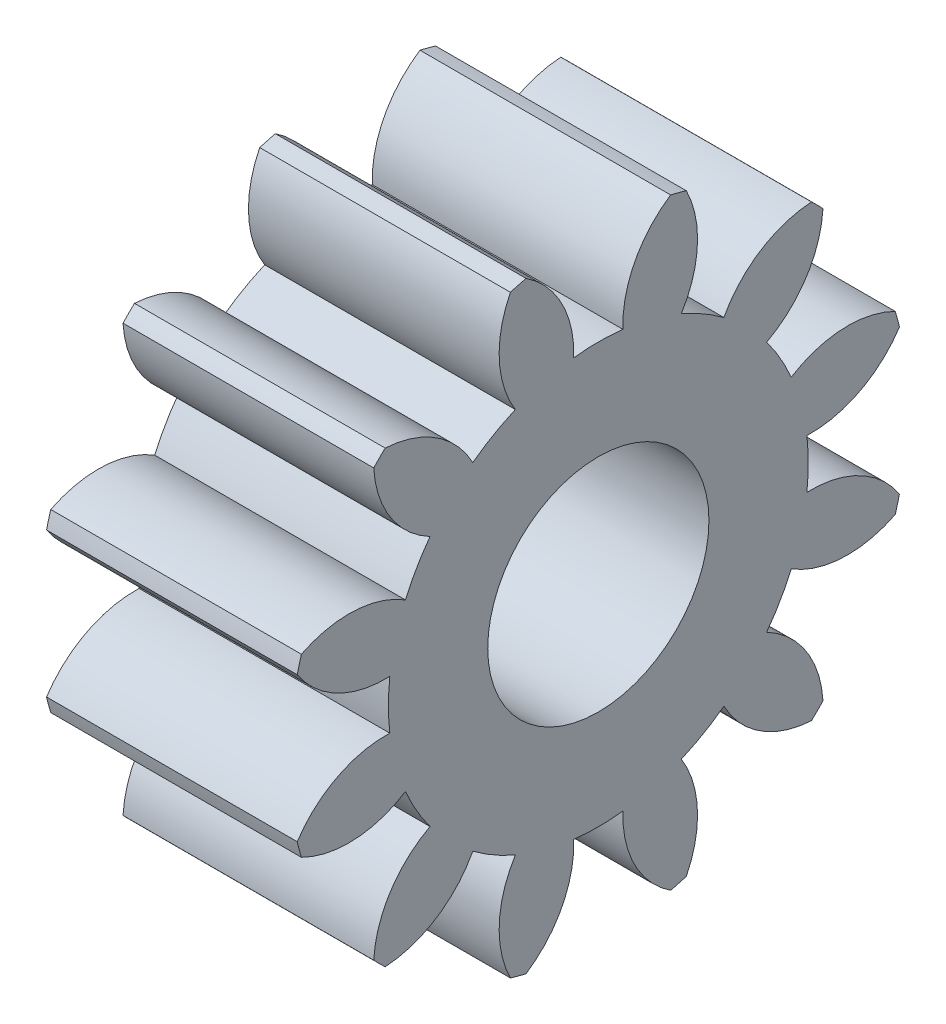
SolidWorks part; units mm, degrees
ref_plane "Plane1" through (0, 0, 0) normal (0, 0, 1) x (1, 0, 0)
ref_plane "Plane2" through (0, 0, 0) normal (0, 1, 0) x (1, 0, 0)
ref_plane "Plane3" through (0, 0, 0) normal (1, 0, 0) x (0, 0, -1)
sketch "HoldingSke" plane through (0, 0, 0) normal (0, 1, 0) x (1, 0, 0)
  line L0 (0, 0) -> (3.2605, -0.693)
  line L1 (-15, 0) -> (100, 0) construction
  line L2 (0, 0) -> (-2.1039, 2.3779)
  line L3 (0, 0) -> (-11.863, 4.5341)
  line L4 (0, 0) -> (8.4473, 1.7955)
  line L5 (0, 0) -> (-46.8476, -17.4728)
  line L6 (0, 0) -> (-1.4092, -0.9508)
  line L7 (-2.1039, 2.3779) -> (8.6586, 51.2059)
  line L8 (-76.2, 54.61) -> (-76, 54.61)
  line L9 (-71.009, 38.7566) -> (-53.1078, 45.2721)
  line L10 (-76.2, 71.12) -> (104.1128, 71.12)
  line L11 (0, 0) -> (-1.7, 0)
  line L12 (-76.2, 101.6) -> (-76.19, 101.6)
  line L13 (24.9733, 27.94) -> (52.9518, 28.4284)
  line L14 (24.9733, 27.94) -> (24.9743, 27.94)
  line L15 (24.9733, 27.94) -> (100.4006, 29.5858)
  line L16 (-63.627, -0.3) -> (-12.827, -0.3)
  circle A0 centre (0, 0) radius 0.75
  circle A1 centre (0, 0) radius 1.424
  circle A2 centre (0, 0) radius 37.5
  circle A3 centre (0, 0) radius 0.75
  dimension "MHD" = 2.848
  dimension "Hub_dia" = 75
  dimension "Bore" = 1.5
  dimension "MBD" = 1.5
  dimension "Num_teeth" = 12
  dimension "Pitch" = 3.3333
  dimension "Overall_len" = 50
  dimension "Show_teeth" = 12
  dimension "Thickness" = 1.7
  dimension "OAL" = 50.0001
  dimension "T_dim" = 0.2
  dimension "Ap" = 20
  dimension "H" = 19.05
  dimension "Pitch_radius" = 180.3128
  dimension "Width" = 1.7
  dimension "Backlash" = 0.01
  dimension "Addendum_fac" = 1
  dimension "Dedendum_fac" = 1.25
  dimension "Clearance_fac" = 0.25
  dimension "Dedendum_add" = 0.001
  dimension "Module" = 0.3
sketch "BasProSke" plane through (0, 0, 0) normal (0, 1, 0) x (1, 0, 0)
  line L0 (-10, 0) -> (60, 0) construction
  line L1 (0, 0) -> (0, 2.1)
  line L2 (0, 0) -> (1.7, 0)
  line L3 (1.7, 0) -> (1.7, 2.1)
  line L4 (1.7, 2.1) -> (0, 2.1)
  dimension "Thickness" = 1.7
  dimension "Diameter" = 4.2
revolve "Base-Revolve" add sketch "BasProSke" angle 360 about L0
sketch "TooCutSke" plane through (0, 0, 0) normal (1, 0, 0) x (0, 0, -1)
  line L1 (0, 0) -> (0, 107) construction
  line L2 (0, 0) -> (-0.2524, 1.7822) construction
  line L3 (0, 0) -> (-0.9249, 3.4519) construction
  line L4 (-0.2524, 1.7822) -> (-0.4625, 1.7259) construction
  arc A0 (0.1667, 1.4142) -> (-0.1667, 1.4142) centre (0, 0) ccw
  arc A1 (0.5203, 2.0607) -> (-0.5203, 2.0607) centre (0, 0) ccw
  circle A2 centre (0, 0) radius 1.8 construction
  circle A3 centre (0, 0) radius 1.6914 construction
  arc A4 (-0.1667, 1.4142) -> (-0.5203, 2.0607) centre (-0.8863, 1.4407) ccw
  arc A5 (0.5203, 2.0607) -> (0.1667, 1.4142) centre (0.8863, 1.4407) ccw
  dimension "Root_dia" = 2.848
  dimension "Overcut_dia" = 4.2508
  dimension "Pitch_dia" = 3.6
  dimension "Base_dia" = 3.3829
  dimension "Flank_rad" = 0.72
  dimension "Half_ang" = 15
  dimension "Half_CT" = 0.2174
extrude "ToothCut" cut sketch "TooCutSke" along normal through all
fillet "Breaks" [suppressed] radius 0.006
fillet "RootFillets" [suppressed] radius 0.076
pattern_circular "TeethCuts" count 12 every 30 about axis through (-10, 0, 0) along (1, 0, 0) of "ToothCut", "RootFillets", "Breaks"
sketch "HubNeaOneSke" plane through (0, 0, 0) normal (-1, 0, 0) x (0, 0, 1)
  circle A0 centre (0, 0) radius 1.424
  dimension "Diameter" = 2.848
extrude "HubNearOne" [suppressed] add sketch "HubNeaOneSke" along normal blind 48.3001
sketch "HubNeaBotSke" plane through (0, 0, 0) normal (-1, 0, 0) x (0, 0, 1)
  circle A0 centre (0, 0) radius 1.424
  dimension "Diameter" = 2.848
extrude "HubNearBoth" [suppressed] add sketch "HubNeaBotSke" along normal blind 24.15
ref_plane "FarPln" through (1.7, 0, 0) normal (1, 0, 0) x (0, 0, -1)
sketch "HubFarSke" plane through (1.7, 0, 0) normal (1, 0, 0) x (0, 0, -1)
  circle A0 centre (0, 0) radius 1.424
  dimension "Diameter" = 2.848
extrude "HubFar" [suppressed] add sketch "HubFarSke" along normal blind 24.15
sketch "BorSke" plane through (0, 0, 0) normal (1, 0, 0) x (0, 0, -1)
  circle A0 centre (0, 0) radius 0.75
  dimension "Diameter" = 1.5
extrude "Bore" cut sketch "BorSke" along normal mid plane 100.0001
sketch "KeySke" plane through (0, 0, 0) normal (1, 0, 0) x (0, 0, -1)
  line L0 (-0.3, 0) -> (-0.3, 0.95)
  line L1 (-0.3, 0.95) -> (0.3, 0.95)
  line L2 (0.3, 0.95) -> (0.3, 0)
  line L3 (0, 0) -> (0, 34) construction
  line L4 (-0.3, 0) -> (0.3, 0)
  dimension "Offset" = 0.95
  dimension "Width" = 0.6
extrude "Keyway" [suppressed] cut sketch "KeySke" along normal mid plane 100.0001
pattern_circular "Keyway2" [suppressed] count 2 every 90 about axis through (-10, 0, 0) along (1, 0, 0)
equation "' \"Module@HoldingSke\" = 6.35"
equation "' \"Num_teeth@HoldingSke\" = 12"
equation "' \"Ap@HoldingSke\" =  20"
equation "' \"Ap@HoldingSke\" = 20"
equation "' \"Width@HoldingSke\" = 0.5 * 25.4"
equation "' \"Hub_dia@HoldingSke\"= 1 * 25.4"
equation "' \"Hub_dia@HoldingSke\" = 1 * 25.4"
equation "' \"Overall_len@HoldingSke\" = 1.0 * 25.4"
equation "' \"Bore@HoldingSke\" = 0.75 * 25.4"
equation "' \"T_dim@HoldingSke\" = 0.1 * 25.4"
equation "' \"Width@KeySke\" = 0.25 * 25.4"
equation "' \"Show_teeth@HoldingSke\" = 13"
equation "' \"Backlash@HoldingSke\" = 0.009 * 25.4"
equation "' \"Addendum_fac@HoldingSke\" = 1.0"
equation "' \"Dedendum_fac@HoldingSke\" = 1.25"
equation "' \"Dedendum_add@HoldingSke\" = 0.00005 * 25.4"
equation "' \"Clearance_fac@HoldingSke\" = 0.25"
equation "\"Pitch@HoldingSke\" = 1 / \"Module@HoldingSke\""
equation "\"Overcut_dia@TooCutSke\" = (\"Num_teeth@HoldingSke\" + 2 * \"Addendum_fac@HoldingSke\") / \"Pitch@HoldingSke\" + 0.002 * 25.4"
equation "\"Pitch_dia@TooCutSke\" = \"Num_teeth@HoldingSke\" / \"Pitch@HoldingSke\""
equation "\"Base_dia@TooCutSke\" = \"Num_teeth@HoldingSke\" / \"Pitch@HoldingSke\" * cos((\"Ap@HoldingSke\"  * 3.14159265 / 180))"
equation "\"Root_dia@TooCutSke\" = (\"Num_teeth@HoldingSke\" + 2) / \"Pitch@HoldingSke\" - 2 * (\"Addendum_fac@HoldingSke\" + \"Dedendum_fac@HoldingSke\") / \"Pitch@HoldingSke\" - \"Dedendum_add@HoldingSke\" * 2"
equation "\"Half_ang@TooCutSke\" = 180 / \"Num_teeth@HoldingSke\""
equation "\"Half_CT@TooCutSke\" = \"Num_teeth@HoldingSke\" / \"Pitch@HoldingSke\" * sin((3.14159265 / 2 / \"Num_teeth@HoldingSke\")) / 2 - 7 * \"Backlash@HoldingSke\" / 4"
equation "\"Flank_rad@TooCutSke\" = \"Num_teeth@HoldingSke\" / \"Pitch@HoldingSke\" / 5"
equation "\"Radius@RootFillets\" = \"Clearance_fac@HoldingSke\" / \"Pitch@HoldingSke\" + \"Dedendum_add@HoldingSke\""
equation "\"Break_rad@Breaks\" = 0.02 / \"Pitch@HoldingSke\""
equation "\"Thickness@HoldingSke\" = \"Width@HoldingSke\""
equation "\"OAL@HoldingSke\" = \"Thickness@HoldingSke\""
equation "\"MHD@HoldingSke\" = (\"Num_teeth@HoldingSke\" + 2) / \"Pitch@HoldingSke\" - 2 * (\"Addendum_fac@HoldingSke\" + \"Dedendum_fac@HoldingSke\")  / \"Pitch@HoldingSke\" - \"Dedendum_add@HoldingSke\" * 2"
equation "\"MBD@HoldingSke\" = (\"Num_teeth@HoldingSke\" + 2) / \"Pitch@HoldingSke\" - 2 * (\"Addendum_fac@HoldingSke\" + \"Dedendum_fac@HoldingSke\")  / \"Pitch@HoldingSke\" - \"Dedendum_add@HoldingSke\" * 2 - 0.002 * 25.4"
equation "\"MHD@HoldingSke\" = ((sgn( \"MHD@HoldingSke\" - \"Hub_dia@HoldingSke\" )-1)*( \"MHD@HoldingSke\" - \"Hub_dia@HoldingSke\" ))/-2+ \"Hub_dia@HoldingSke\""
equation "\"MBD@HoldingSke\" = ((sgn( \"MBD@HoldingSke\" - \"Bore@HoldingSke\" )-1)*( \"MBD@HoldingSke\" - \"Bore@HoldingSke\" ))/-2+ \"Bore@HoldingSke\""
equation "\"OAL@HoldingSke\" = ((sgn( \"OAL@HoldingSke\" - \"Overall_len@HoldingSke\" )+1)*( \"OAL@HoldingSke\" - \"Overall_len@HoldingSke\" ))/2 + \"Overall_len@HoldingSke\" + 0.000002 * 25.4"
equation "\"Num_teeth@TeethCuts\" = int( \"Show_teeth@HoldingSke\" ) + 1"
equation "\"Num_teeth@TeethCuts\" = ((sgn( \"Num_teeth@TeethCuts\" - \"Num_teeth@HoldingSke\" )-1)*( \"Num_teeth@TeethCuts\" - \"Num_teeth@HoldingSke\" ))/-2+ \"Num_teeth@HoldingSke\""
equation "\"Num_teeth@TeethCuts\" = ((sgn( \"Num_teeth@TeethCuts\" - 2.0)+1)*( \"Num_teeth@TeethCuts\" - 2.0))/2 +2.0"
equation "\"Angle@TeethCuts\" = 360.0 / \"Num_teeth@HoldingSke\""
equation "\"Diameter@BasProSke\" = (\"Num_teeth@HoldingSke\" + 2 * \"Addendum_fac@HoldingSke\") / \"Pitch@HoldingSke\""
equation "\"Thickness@BasProSke\"  = \"Thickness@HoldingSke\""
equation "' \"Fillet_rad@BasProSke\" =  \"Thickness@HoldingSke\" * 0.05"
equation "' \"Fillet_rad@BasProSke\" = \"Thickness@HoldingSke\" * 0.05"
equation "\"MHD@HoldingSke\" = ((sgn( \"MHD@HoldingSke\" - \"Root_dia@TooCutSke\" )-1)*( \"MHD@HoldingSke\" - \"Root_dia@TooCutSke\" ))/-2+ \"Root_dia@TooCutSke\""
equation "\"Diameter@HubNeaOneSke\" = \"MHD@HoldingSke\""
equation "\"Length@HubNearOne\" = \"OAL@HoldingSke\" - \"Thickness@BasProSke\""
equation "\"Diameter@HubNeaBotSke\" = \"MHD@HoldingSke\""
equation "\"Length@HubNearBoth\" = ( \"OAL@HoldingSke\" - \"Thickness@BasProSke\" ) / 2.0"
equation "\"Thickness@FarPln\" = \"Thickness@BasProSke\""
equation "\"Diameter@HubFarSke\" = \"MHD@HoldingSke\""
equation "\"Length@HubFar\" = ( \"OAL@HoldingSke\" - \"Thickness@BasProSke\" ) / 2.0"
equation "\"Diameter@BorSke\" = \"MBD@HoldingSke\""
equation "\"D1@Bore\" = \"OAL@HoldingSke\" * 2.0"
equation "\"D1@Keyway\" = \"OAL@HoldingSke\" * 2.0"
equation "\"Offset@KeySke\" = \"T_dim@HoldingSke\" + \"MBD@HoldingSke\" / 2.0"
